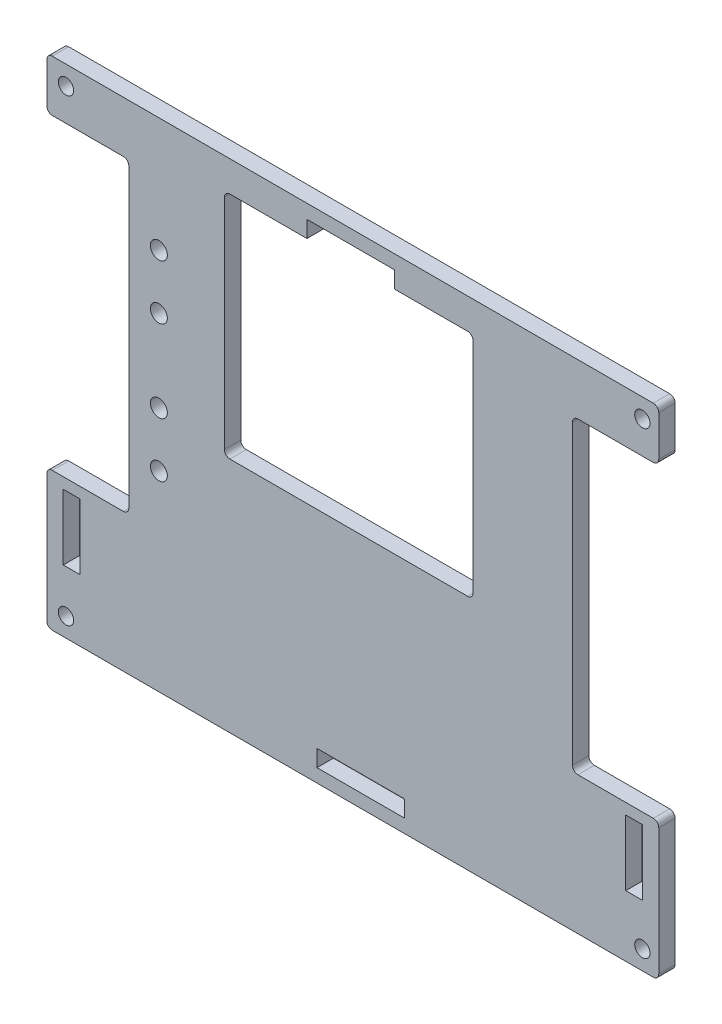
SolidWorks part; units mm, degrees
ref_plane "Alzado" through (0, 0, 0) normal (0, 0, 1) x (1, 0, 0)
ref_plane "Planta" through (0, 0, 0) normal (0, 1, 0) x (1, 0, 0)
ref_plane "Vista lateral" through (0, 0, 0) normal (1, 0, 0) x (0, 0, -1)
sketch "Croquis1" plane through (0, 0, 0) normal (0, 0, 1) x (1, 0, 0)
  line L0 (56, -21.3) -> (56, -44.5)
  line L1 (-55, 45.5) -> (55, 45.5)
  line L2 (-56, 44.5) -> (-56, 37.1)
  line L3 (-55, -45.5) -> (55, -45.5)
  line L4 (56, 44.5) -> (56, 37.1)
  line L5 (-56, 45.5) -> (56, -45.5) construction
  line L6 (-56, -45.5) -> (56, 45.5) construction
  line L7 (55, 36.1) -> (41.2, 36.1)
  line L9 (55, -20.3) -> (41.2, -20.3)
  line L10 (40.2, 35.1) -> (40.2, -19.3)
  line L11 (-56, -21.15) -> (-56, -44.5)
  line L12 (-55, 36.1) -> (-42, 36.1)
  line L14 (-55, -20.15) -> (-42, -20.15)
  line L15 (-41, 35.1) -> (-41, -19.15)
  line L16 (-8.4, 39.9) -> (-22.5, 39.9)
  line L17 (21, -2.1) -> (-22.5, -2.1)
  line L18 (22, -1.1) -> (22, 38.9)
  line L19 (21, 39.9) -> (7.6, 39.9)
  line L20 (-23.5, -1.1) -> (-23.5, 38.9)
  line L22 (-8.4, 39.9) -> (-8.4, 42.95)
  line L23 (-8.4, 42.95) -> (7.6, 42.95)
  line L24 (7.6, 39.9) -> (7.6, 42.95)
  line L26 (-6.55, -40) -> (9.45, -40)
  line L27 (-6.55, -40) -> (-6.55, -43.05)
  line L28 (-6.55, -43.05) -> (9.45, -43.05)
  line L29 (9.45, -40) -> (9.45, -43.05)
  line L30 (49.95, -22.3) -> (53, -22.3)
  line L31 (49.95, -22.3) -> (49.95, -34.3)
  line L32 (49.95, -34.3) -> (53, -34.3)
  line L33 (53, -22.3) -> (53, -34.3)
  line L34 (-49.95, -22.15) -> (-53, -22.15)
  line L35 (-49.95, -22.15) -> (-49.95, -34.15)
  line L36 (-49.95, -34.15) -> (-53, -34.15)
  line L37 (-53, -22.15) -> (-53, -34.15)
  arc A0 (-42, -20.15) -> (-41, -19.15) centre (-42, -19.15) ccw
  arc A1 (-56, -21.15) -> (-55, -20.15) centre (-55, -21.15) cw
  arc A2 (-55, -45.5) -> (-56, -44.5) centre (-55, -44.5) cw
  arc A3 (55, -45.5) -> (56, -44.5) centre (55, -44.5) ccw
  arc A4 (56, -21.3) -> (55, -20.3) centre (55, -21.3) ccw
  arc A5 (41.2, -20.3) -> (40.2, -19.3) centre (41.2, -19.3) cw
  arc A6 (40.2, 35.1) -> (41.2, 36.1) centre (41.2, 35.1) cw
  arc A7 (56, 37.1) -> (55, 36.1) centre (55, 37.1) cw
  arc A8 (56, 44.5) -> (55, 45.5) centre (55, 44.5) ccw
  arc A9 (-41, 35.1) -> (-42, 36.1) centre (-42, 35.1) ccw
  arc A10 (-55, 36.1) -> (-56, 37.1) centre (-55, 37.1) cw
  arc A11 (-55, 45.5) -> (-56, 44.5) centre (-55, 44.5) ccw
  circle A12 centre (-35.5, 24.5) radius 1.55
  circle A13 centre (-35.5, 14.5) radius 1.55
  circle A14 centre (-35.5, -0.5) radius 1.55
  circle A15 centre (-35.5, -10.5) radius 1.55
  arc A16 (22, -1.1) -> (21, -2.1) centre (21, -1.1) cw
  arc A17 (22, 38.9) -> (21, 39.9) centre (21, 38.9) ccw
  arc A18 (-22.5, -2.1) -> (-23.5, -1.1) centre (-22.5, -1.1) cw
  arc A19 (-22.5, 39.9) -> (-23.5, 38.9) centre (-22.5, 38.9) ccw
  point P0 (0, 0)
  point P28 (40.2, -20.3)
  point P31 (40.2, 36.1)
  point P58 (22, -2.1)
  point P63 (-23.5, -2.1)
  point P66 (-23.5, 39.9)
  point P75 (0, 45.5)
  dimension "D9" = 1
  dimension "D10" = 3.1
  dimension "D19" = 1
  dimension "D1" = 112
  dimension "D3" = 25.2
  dimension "D5" = 15.8
  dimension "D7" = 25.35
  dimension "D8" = 15
  dimension "D11" = 5.5
  dimension "D14" = 10
  dimension "D16" = 15
  dimension "D17" = 45.5
  dimension "D18" = 42
  dimension "D20" = 18.2
  dimension "D22" = 3.05
  dimension "D4" = 56.4
  dimension "D6" = 91
  dimension "D12" = 35
  dimension "D21" = 43.4
  dimension "D23" = 14.4
  dimension "D24" = 16
  dimension "D25" = 3.05
  dimension "D26" = 16
  dimension "D27" = 49.45
  dimension "D28" = 2.45
  dimension "D29" = 2.55
  dimension "D30" = 12
  dimension "D31" = 3.05
  dimension "D32" = 3
  dimension "D33" = 2
  dimension "D35" = 12
  dimension "D36" = 2
  dimension "D37" = 3
  dimension "D34" = 3.05
  dimension "D38" = 15.1
  dimension "D39" = 2.55
  dimension "D40" = 11.2
  dimension "D41" = 99.9
  dimension "D13" = 2
  dimension "D15" = 2
extrude "Saliente-Extruir1" add sketch "Croquis1" along normal blind 3
sketch "Croquis2" plane through (0, 0, 3) normal (0, 0, 1) x (1, 0, 0)
  line L0 (55, 45.5) -> (-55, 45.5) construction
  line L1 (56, 37.1) -> (56, 44.5) construction
  line L2 (-56, -21.15) -> (-56, -44.5) construction
  line L4 (-55, -45.5) -> (55, -45.5) construction
  line L5 (-56, 44.5) -> (-56, 37.1) construction
  line L6 (56, -44.5) -> (56, -21.3) construction
  circle A0 centre (53, 42) radius 1.4
  circle A1 centre (-52.5, 42) radius 1.4
  circle A2 centre (-52.5, -42) radius 1.4
  circle A3 centre (53, -42) radius 1.4
  dimension "D3" = 2.8
  dimension "D4" = 3.5
  dimension "D5" = 3
  dimension "D6" = 84
  dimension "D7" = 105.5
  dimension "D8" = 3.5
  dimension "D9" = 3.5
  dimension "D10" = 3.5
  dimension "D11" = 3.5
  dimension "D12" = 3
  dimension "D13" = 3.5
  dimension "D1" = 2
  dimension "D2" = 2
extrude "Cortar-Extruir2" cut sketch "Croquis2" against normal through all
equation "\"Diam\"= 2.8"
equation "\"D3@Croquis2\"=\"Diam\""
equation "\"Espes\"= 3.05"
equation "\"D34@Croquis1\"=\"Espes\""
equation "\"D31@Croquis1\"=\"Espes\""
equation "\"D25@Croquis1\"=\"Espes\""
equation "\"D22@Croquis1\"=\"Espes\""
